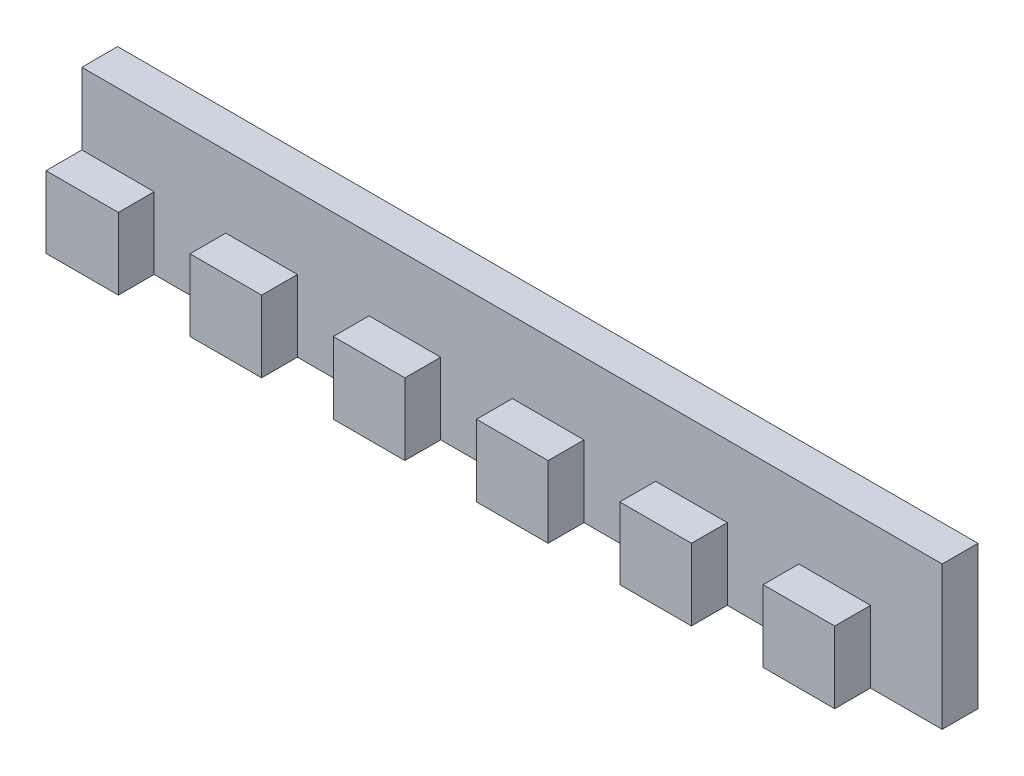
SolidWorks part; units mm, degrees
ref_plane "Спереди" through (0, 0, 0) normal (0, 0, 1) x (1, 0, 0)
ref_plane "Сверху" through (0, 0, 0) normal (0, 1, 0) x (1, 0, 0)
ref_plane "Справа" through (0, 0, 0) normal (1, 0, 0) x (0, 0, -1)
sketch "Эскиз1" plane through (0, 0, 0) normal (0, 1, 0) x (1, 0, 0)
  line L0 (0, 0) -> (10.0994, 0)
  line L1 (10.0994, 0) -> (10.0994, 5)
  line L2 (10.0994, 5) -> (20.0994, 5)
  line L3 (0, 10) -> (0, 0)
  line L4 (20.0994, 5) -> (20.0994, 0)
  line L5 (20.0994, 0) -> (30.0994, 0)
  line L13 (120.0994, 10) -> (0, 10)
  line L44 (120.0994, 5) -> (120.0994, 10)
  line L45 (30.0994, 0) -> (30.0994, 5)
  line L46 (30.0994, 5) -> (40.0994, 5)
  line L47 (40.0994, 5) -> (40.0994, 0)
  line L48 (40.0994, 0) -> (50.0994, 0)
  line L49 (50.0994, 0) -> (50.0994, 5)
  line L50 (50.0994, 5) -> (60.0994, 5)
  line L51 (60.0994, 5) -> (60.0994, 0)
  line L52 (60.0994, 0) -> (70.0994, 0)
  line L53 (70.0994, 0) -> (70.0994, 5)
  line L54 (70.0994, 5) -> (80.0994, 5)
  line L55 (80.0994, 5) -> (80.0994, 0)
  line L56 (80.0994, 0) -> (90.0994, 0)
  line L57 (90.0994, 0) -> (90.0994, 5)
  line L58 (90.0994, 5) -> (100.0994, 5)
  line L59 (100.0994, 5) -> (100.0994, 0)
  line L60 (100.0994, 0) -> (110.0994, 0)
  line L73 (110.0994, 0) -> (110.0994, 5)
  line L74 (110.0994, 5) -> (120.0994, 5)
  point P4 (111.4206, 0)
  dimension "D1" = 5
extrude "Бобышка-Вытянуть1" add sketch "Эскиз1" along normal blind 20
sketch "Эскиз2" plane through (0, 0, 0) normal (-1, 0, 0) x (0, 0, 1)
  line L0 (-10, 20) -> (0, 20) construction
  line L1 (-5, 20) -> (0, 20)
  line L2 (-5, 20) -> (-5, 10)
  line L3 (-5, 10) -> (0, 10)
  line L4 (0, 20) -> (0, 10)
  line L5 (0, 20) -> (0, 0) construction
extrude "Вырез-Вытянуть1" cut sketch "Эскиз2" against normal through all
